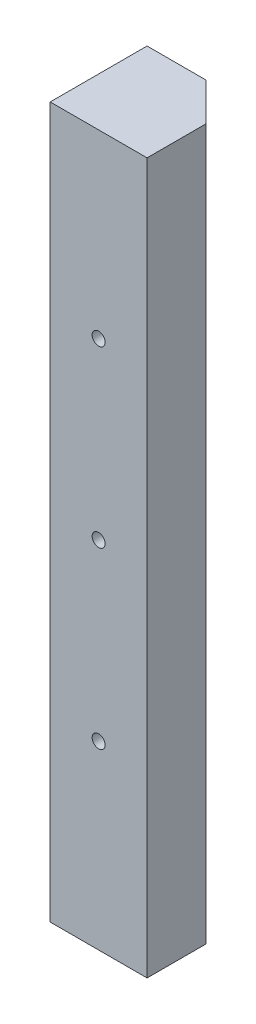
SolidWorks part; units mm, degrees
material "AISI 1020"
ref_plane "Front Plane" through (0, 0, 0) normal (0, 0, 1) x (1, 0, 0)
ref_plane "Top Plane" through (0, 0, 0) normal (0, 1, 0) x (1, 0, 0)
ref_plane "Right Plane" through (0, 0, 0) normal (1, 0, 0) x (0, 0, -1)
sketch "Sketch1" plane through (0, 0, 0) normal (0, 1, 0) x (1, 0, 0)
  line L3 (-12.1104, -25) -> (25.9896, -25)
  line L5 (-12.1104, 13.1) -> (25.9896, 13.1)
  line L6 (25.9896, 13.1) -> (25.9896, -25)
  line L7 (-12.1104, 13.1) -> (-12.1104, -25)
  point P0 (0, 0)
  dimension "D1" = 38.1
  dimension "D2" = 38.1
extrude "Boss-Extrude1" add sketch "Sketch1" along normal blind 279.4
chamfer "Chamfer1" distance 15 angle 45 1 edges at (25.9896, 139.7, -13.1)
sketch "Sketch15" plane through (12.0448, 0, -12.0448) normal (0.7071, 0, -0.7071) x (-0.7071, 0, -0.7071)
  line L0 (-9.1143, 279.4) -> (-9.1143, 0) construction
  line L1 (-19.7209, 279.4) -> (1.4923, 279.4) construction
  line L2 (1.4923, 0) -> (-19.7209, 0) construction
  circle A0 centre (-9.1143, 238.76) radius 6.35
  circle A1 centre (-9.1143, 177.8) radius 6.35
  circle A2 centre (-9.1143, 101.6) radius 6.35
  circle A3 centre (-9.1143, 40.64) radius 6.35
  dimension "D1" = 12.7
  dimension "D3" = 12.7
  dimension "D4" = 12.7
  dimension "D5" = 12.7
  dimension "D2" = 40.64
  dimension "D6" = 60.96
  dimension "D7" = 76.2
  dimension "D8" = 60.96
extrude "Cut-Extrude2" cut sketch "Sketch15" against normal blind 25
ref_plane "Plane1" through (0, 0, -13.1) normal (0, 0, -1) x (-1, 0, 0)
sketch "Sketch23" plane through (0, 0, 25) normal (0, 0, 1) x (1, 0, 0)
  line L0 (-12.1104, 279.4) -> (25.9896, 279.4) construction
  point P0 (6.9396, 208.28)
  point P1 (6.9396, 139.7)
  point P2 (6.9396, 71.12)
  point P5 (6.9396, 279.4)
  dimension "D1" = 139.7
  dimension "D2" = 68.58
  dimension "D3" = 68.58
hole_wizard "1/4-20 Tapped Hole1" positions "Sketch24" profile "Sketch25" tap size "1/4-20" standard "ANSI Inch"
sketch "Sketch24" plane through (0, 0, 25) normal (0, 0, 1) x (1, 0, 0)
  point P0 (6.9396, 208.28)
  point P3 (6.9396, 139.7)
  point P6 (6.9396, 71.12)
sketch "Sketch25" plane through (6.9396, 208.28, 25) normal (1, 0, 0) x (0, -1, 0)
  line L0 (0, 0) -> (0, 21.8538)
  line L1 (0, 21.8538) -> (2.5527, 20.32)
  line L2 (2.5527, 20.32) -> (2.5527, 0)
  line L5 (2.5527, 0) -> (0, 0)
  line L10 (0, 21.8538) -> (-2.5527, 20.32) construction
  line L11 (0, -6.35) -> (0, 107.95) construction
  dimension "Tap Drill Dia." = 5.1054
  dimension "Tap Drill Depth" = 20.32
  dimension "Drill Angle" = 118
cosmetic thread "Hole Thread2" parameters "D1"=17.78, "D2"=6.35
cosmetic thread "Hole Thread3" parameters "D1"=17.78, "D2"=6.35
cosmetic thread "Hole Thread4" parameters "D1"=17.78, "D2"=6.35
sketch "Sketch26" plane through (0, 0, -13.1) normal (0, 0, -1) x (-1, 0, 0)
  line L1 (-0.8119, 40.64) -> (-18.4896, 40.64) construction
  line L2 (-10.9896, 279.4) -> (-10.9896, 0) construction
  line L3 (-0.8119, 101.6) -> (-18.4896, 101.6) construction
  line L4 (-0.8119, 177.8) -> (-18.4896, 177.8) construction
  line L6 (-0.8119, 238.76) -> (-18.4896, 238.76) construction
  point P0 (-7.1796, 40.64)
  point P1 (-7.1796, 101.6)
  point P4 (-7.1796, 177.8)
  point P5 (-7.1796, 238.76)
  dimension "D1" = 3.81
hole_wizard "#8-32 Tapped Hole1" positions "Sketch29" profile "Sketch30" tap size "#8-32" standard "ANSI Inch"
sketch "Sketch29" plane through (0, 0, -13.1) normal (0, 0, -1) x (-1, 0, 0)
  point P0 (-7.1796, 40.64)
  point P4 (-7.1796, 101.6)
  point P7 (-7.1796, 177.8)
  point P10 (-7.1796, 238.76)
sketch "Sketch30" plane through (7.1796, 40.64, -13.1) normal (1, 0, 0) x (0, 1, 0)
  line L0 (0, 0) -> (0, 9.8297)
  line L1 (0, 9.8297) -> (1.7272, 9.8297)
  line L2 (1.7272, 9.8297) -> (1.7272, 0)
  line L5 (1.7272, 0) -> (0, 0)
  line L11 (0, -6.35) -> (0, 107.95) construction
  dimension "Thru Tap Drill Dia." = 3.4544
  dimension "Thru Tap Drill Depth" = 9.8297
cosmetic thread "Hole Thread5" parameters "D2"=4.1656
cosmetic thread "Hole Thread6" parameters "D2"=4.1656
cosmetic thread "Hole Thread7" parameters "D2"=4.1656
cosmetic thread "Hole Thread8" parameters "D2"=4.1656
